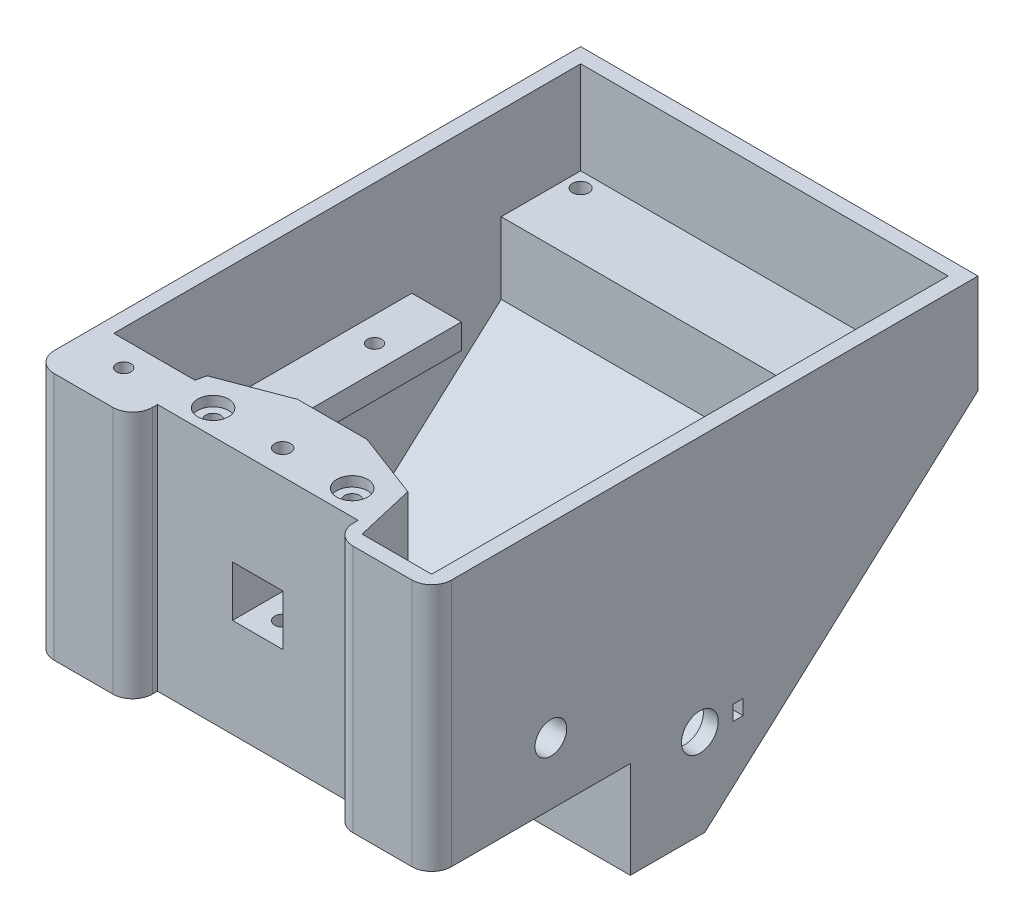
SolidWorks part; units mm, degrees
ref_plane "Спереди" through (0, 0, 0) normal (0, 0, 1) x (1, 0, 0)
ref_plane "Сверху" through (0, 0, 0) normal (0, 1, 0) x (1, 0, 0)
ref_plane "Справа" through (0, 0, 0) normal (1, 0, 0) x (0, 0, -1)
sketch "Sketch2" plane through (0, 0, 0) normal (1, 0, 0) x (0, 0, -1)
  line L0 (-27.3205, 20.9982) -> (-27.3205, -29.0018)
  line L1 (-27.3205, -29.0018) -> (12.6795, -29.0018)
  line L2 (12.6795, -29.0018) -> (12.6795, -48.5114)
  line L3 (12.6795, -48.5114) -> (27.6795, -48.5114)
  line L4 (82.6795, 20.9982) -> (82.6795, 0.9982)
  line L5 (82.6795, 20.9982) -> (-27.3205, 20.9982)
  line L6 (82.6795, 0.9982) -> (27.6795, -48.5114)
  dimension "D1" = 110
  dimension "D2" = 50
  dimension "D3" = 40
  dimension "D4" = 15
  dimension "D5" = 20
extrude "Boss-Extrude1" add sketch "Sketch2" along normal blind 80
shell "Shell1" thickness 3
sketch "Sketch3" plane through (0, 0, 24.3205) normal (0, 0, -1) x (-1, 0, 0)
  line L0 (-40, 20.9982) -> (-40, -26.0018) construction
  line L3 (-77, 20.9982) -> (-3, 20.9982) construction
  line L4 (-77, -26.0018) -> (-3, -26.0018) construction
  line L6 (-17, 20.9982) -> (-63, 20.9982)
  line L7 (-17, 20.9982) -> (-17, -26.0018)
  line L8 (-17, -26.0018) -> (-63, -26.0018)
  line L9 (-63, 20.9982) -> (-63, -26.0018)
  line L10 (-17, 20.9982) -> (-63, -26.0018) construction
  line L11 (-17, -26.0018) -> (-63, 20.9982) construction
  point P6 (-40, -2.5018)
  dimension "D1" = 46
extrude "Boss-Extrude2" add sketch "Sketch3" along normal blind 17
sketch "Sketch4" plane through (0, 0, 27.3205) normal (0, 0, 1) x (1, 0, 0)
  line L0 (0, 20.9982) -> (80, -29.0018) construction
  line L2 (45.1, -9.1018) -> (34.9, -9.1018)
  line L3 (45.1, -9.1018) -> (45.1, 1.0982)
  line L4 (45.1, 1.0982) -> (34.9, 1.0982)
  line L5 (34.9, -9.1018) -> (34.9, 1.0982)
  line L6 (45.1, -9.1018) -> (34.9, 1.0982) construction
  line L7 (45.1, 1.0982) -> (34.9, -9.1018) construction
  point P4 (40, -4.0018)
  dimension "D1" = 10.2
extrude "Cut-Extrude1" cut sketch "Sketch4" against normal up to surface (20 mm away) up to face at (40, -2.5018, 7.3205)
sketch "Sketch6" plane through (0, -29.0018, 0) normal (0, -1, 0) x (1, 0, 0)
  line L0 (40, 27.3205) -> (40, -12.6795) construction
  line L1 (47.5, -5.4795) -> (32.5, -5.4795)
  line L2 (47.5, -5.4795) -> (47.5, 7.3205)
  line L3 (47.5, 7.3205) -> (32.5, 7.3205)
  line L4 (32.5, -5.4795) -> (32.5, 7.3205)
  line L5 (47.5, -5.4795) -> (32.5, 7.3205) construction
  line L6 (47.5, 7.3205) -> (32.5, -5.4795) construction
  line L7 (80, -12.6795) -> (0, -12.6795) construction
  line L9 (80, 27.3205) -> (0, 27.3205) construction
  point P0 (40, 0.9205)
  dimension "D1" = 15
  dimension "D2" = 12.8
  dimension "D4" = 20
extrude "Cut-Extrude2" cut sketch "Sketch6" against normal up to surface (3 mm away) up to face at (40, -26.0018, 10.0705)
sketch "Sketch7" plane through (0, 0, 27.3205) normal (0, 0, 1) x (1, 0, 0)
  line L0 (40, 20.9982) -> (40, -29.0018) construction
  line L1 (80, 20.9982) -> (0, 20.9982) construction
  line L2 (80, -29.0018) -> (0, -29.0018) construction
  line L4 (60.2, -29.0018) -> (19.8, -29.0018)
  line L5 (60.2, -29.0018) -> (60.2, 20.9982)
  line L6 (60.2, 20.9982) -> (19.8, 20.9982)
  line L7 (19.8, -29.0018) -> (19.8, 20.9982)
  line L8 (60.2, -29.0018) -> (19.8, 20.9982) construction
  line L9 (60.2, 20.9982) -> (19.8, -29.0018) construction
  point P6 (40, -4.0018)
  dimension "D1" = 40.4
extrude "Cut-Extrude3" cut sketch "Sketch7" against normal blind 5
fillet "Fillet1" radius 4 4 edges at (19.8, -4.0018, 27.3205) (60.2, -4.0018, 27.3205) (80, -4.0018, 27.3205) (0, -4.0018, 27.3205)
sketch "Sketch12" plane through (0, 20.9982, 0) normal (0, 1, 0) x (1, 0, 0)
  line L0 (19.8, -22.3205) -> (19.8, -12.3205) construction
  line L1 (19.8, -12.3205) -> (60.2, -12.3205) construction
  line L2 (60.2, -12.3205) -> (60.2, -22.3205) construction
  line L3 (33, -7.3205) -> (19.8, -12.3205)
  line L4 (17, -7.3205) -> (63, -7.3205) construction
  line L5 (19.8, -12.3205) -> (17, -24.3205)
  line L6 (17, -24.3205) -> (17, -7.3205)
  line L7 (17, -7.3205) -> (33, -7.3205)
  line L8 (47, -7.3205) -> (63, -7.3205)
  line L9 (63, -7.3205) -> (63, -24.3205)
  line L10 (63, -24.3205) -> (60.2, -12.3205)
  line L11 (60.2, -12.3205) -> (47, -7.3205)
  dimension "D1" = 10
  dimension "D2" = 16
extrude "Cut-Extrude7" cut sketch "Sketch12" against normal up to surface (47 mm away) up to face at (40, -26.0018, 7.0205)
sketch "Sketch13" plane through (0, 20.9982, 0) normal (0, 1, 0) x (1, 0, 0)
  line L0 (19.8, -22.3205) -> (19.8, -12.3205) construction
  line L1 (19.8, -12.3205) -> (60.2, -12.3205) construction
  line L2 (60.2, -12.3205) -> (60.2, -22.3205) construction
  line L3 (60.2, -17.3205) -> (19.8, -17.3205) construction
  circle A0 centre (26, -17.3205) radius 1.5
  circle A1 centre (54, -17.3205) radius 1.5
  point P14 (40, -17.3205)
  dimension "D1" = 3
  dimension "D2" = 28
  dimension "D3" = 14
  dimension "D4" = 6.2
extrude "Cut-Extrude8" cut sketch "Sketch13" against normal blind 25
sketch "Sketch14" plane through (0, 20.9982, 0) normal (0, 1, 0) x (1, 0, 0)
  circle A0 centre (26, -17.3205) radius 3.1
  circle A1 centre (54, -17.3205) radius 3.1
  dimension "D1" = 6.2
extrude "Cut-Extrude9" cut sketch "Sketch14" against normal blind 2
sketch "Sketch17" plane through (77, 0, 0) normal (-1, 0, 0) x (0, 0, 1)
  line L0 (-45.6795, -2.0018) -> (-0.6795, -2.0018)
  line L1 (-0.6795, -2.0018) -> (-0.6795, -7.0018)
  line L2 (-0.6795, -7.0018) -> (-45.6795, -7.0018)
  line L3 (-45.6795, -7.0018) -> (-45.6795, -2.0018)
  line L4 (-79.6795, 20.9982) -> (24.3205, 20.9982) construction
  line L5 (-79.6795, 2.3342) -> (-79.6795, 20.9982) construction
  dimension "D1" = 45
  dimension "D2" = 5
  dimension "D3" = 23
  dimension "D4" = 34
extrude "Boss-Extrude5" add sketch "Sketch17" along normal up to surface (74 mm away) up to face at (3, -14.0994, -24.0865)
sketch "Sketch18" plane through (0, -2.0018, 0) normal (0, 1, 0) x (1, 0, 0)
  line L0 (40, 0.6795) -> (40, 45.6795) construction
  line L1 (3, 0.6795) -> (77, 0.6795) construction
  line L2 (3, 45.6795) -> (77, 45.6795) construction
  line L3 (77, 0.6795) -> (77, 45.6795) construction
  line L4 (13, 0.6795) -> (67, 0.6795)
  line L5 (13, 0.6795) -> (13, 45.6795)
  line L6 (13, 45.6795) -> (67, 45.6795)
  line L7 (67, 0.6795) -> (67, 45.6795)
  line L8 (13, 0.6795) -> (67, 45.6795) construction
  line L9 (13, 45.6795) -> (67, 0.6795) construction
  point P6 (40, 23.1795)
  dimension "D1" = 10
extrude "Cut-Extrude10" cut sketch "Sketch18" against normal up to next
sketch "Sketch19" plane through (0, -2.0018, 0) normal (0, 1, 0) x (1, 0, 0)
  line L0 (72, 45.6795) -> (72, 0.6795) construction
  line L1 (67, 45.6795) -> (77, 45.6795) construction
  line L2 (67, 0.6795) -> (77, 0.6795) construction
  line L3 (8, 45.6795) -> (8, 0.6795) construction
  line L4 (3, 45.6795) -> (13, 45.6795) construction
  line L5 (3, 0.6795) -> (13, 0.6795) construction
  circle A0 centre (72, 37.1795) radius 1.45
  circle A1 centre (72, 6.1795) radius 1.45
  circle A2 centre (8, 33.1795) radius 1.45
  circle A3 centre (8, 6.1795) radius 1.45
  point P20 (72, 23.1795)
  point P21 (8, 23.1795)
  dimension "D1" = 2.9
  dimension "D2" = 14
  dimension "D3" = 17
  dimension "D4" = 17
  dimension "D5" = 10
extrude "Cut-Extrude11" cut sketch "Sketch19" against normal up to next
sketch "Sketch21" plane through (0, -26.0018, 0) normal (0, 1, 0) x (1, 0, 0)
  line L0 (3, -24.3205) -> (3, -14.3205)
  line L1 (3, -24.3205) -> (3, 15.6795) construction
  line L2 (3, -14.3205) -> (19.3333, -14.3205)
  line L3 (19.8, -12.3205) -> (17, -24.3205) construction
  line L4 (19.3333, -14.3205) -> (17, -24.3205)
  line L6 (3, -24.3205) -> (17, -24.3205)
  dimension "D1" = 10
extrude "Boss-Extrude6" add sketch "Sketch21" along normal up to surface (47 mm away) up to face at (54, 20.9982, 20.4205)
sketch "Sketch22" plane through (0, 20.9982, 0) normal (0, 1, 0) x (1, 0, 0)
  line L0 (0, 82.6795) -> (0, -23.3205) construction
  line L1 (15.8, -27.3205) -> (4, -27.3205) construction
  circle A0 centre (10, -19.3205) radius 1.45
  dimension "D1" = 2.9
  dimension "D2" = 10
  dimension "D3" = 8
extrude "Cut-Extrude12" cut sketch "Sketch22" against normal through all
sketch "Sketch24" plane through (80, 0, 0) normal (1, 0, 0) x (0, 0, -1)
  line L0 (12.6795, -48.5114) -> (27.6795, -48.5114) construction
  line L1 (12.6795, -29.0018) -> (12.6795, -48.5114) construction
  line L2 (18.1795, -30.5114) -> (18.1795, -19.0114) construction
  line L3 (18.1795, -19.0114) -> (35.1795, -19.0114) construction
  line L4 (35.1795, -19.0114) -> (35.1795, -30.5114) construction
  line L5 (26.6795, -19.0114) -> (26.6795, -39.0114) construction
  line L6 (30.3795, -30.5114) -> (34.3795, -30.5114) construction
  line L8 (33.3795, -32.0114) -> (35.3795, -32.0114)
  line L9 (33.3795, -32.0114) -> (33.3795, -29.0114)
  line L10 (33.3795, -29.0114) -> (35.3795, -29.0114)
  line L11 (35.3795, -32.0114) -> (35.3795, -29.0114)
  line L12 (33.3795, -32.0114) -> (35.3795, -29.0114) construction
  line L13 (33.3795, -29.0114) -> (35.3795, -32.0114) construction
  circle A0 centre (26.6795, -30.5114) radius 3.7
  circle A1 centre (26.6795, -30.5114) radius 8.5 construction
  dimension "D1" = 7.4
  dimension "D2" = 17
  dimension "D3" = 18
  dimension "D4" = 14
  dimension "D5" = 20
  dimension "D6" = 4
  dimension "D7" = 2
  dimension "D8" = 3
extrude "Cut-Extrude13" cut sketch "Sketch24" against normal up to next
sketch "Sketch26" plane through (3, 0, 0) normal (1, 0, 0) x (0, 0, -1)
  line L0 (79.6795, 2.3342) -> (63.6795, 2.3342)
  line L1 (63.6795, 2.3342) -> (63.6795, -12.0686)
  line L2 (26.5281, -45.5114) -> (79.6795, 2.3342) construction
  line L3 (63.6795, -12.0686) -> (79.6795, 2.3342)
  dimension "D1" = 16
extrude "Boss-Extrude7" add sketch "Sketch26" along normal up to surface (74 mm away) up to face at (77, -30.5114, -34.3795)
sketch "Sketch27" plane through (0, 2.3342, 0) normal (0, 1, 0) x (1, 0, 0)
  line L0 (3, 76.6795) -> (77, 76.6795) construction
  line L1 (3, 79.6795) -> (3, 63.6795) construction
  line L2 (77, 79.6795) -> (77, 63.6795) construction
  line L3 (80, 82.6795) -> (0, 82.6795) construction
  circle A0 centre (6, 76.6795) radius 1.65
  circle A1 centre (74, 76.6795) radius 1.65
  point P10 (40, 76.6795)
  dimension "D1" = 3.3
  dimension "D2" = 68
  dimension "D3" = 34
  dimension "D4" = 6
extrude "Cut-Extrude14" cut sketch "Sketch27" against normal blind 10
sketch "Sketch28" plane through (0, 2.3342, 0) normal (0, 1, 0) x (1, 0, 0)
  line L1 (74, 79.9295) -> (71.1854, 78.3045)
  line L2 (71.1854, 78.3045) -> (71.1854, 75.0545)
  line L3 (71.1854, 75.0545) -> (74, 73.4295)
  line L4 (74, 73.4295) -> (76.8146, 75.0545)
  line L5 (76.8146, 75.0545) -> (76.8146, 78.3045)
  line L6 (76.8146, 78.3045) -> (74, 79.9295)
  line L7 (6, 73.4295) -> (8.8146, 75.0545)
  line L8 (8.8146, 75.0545) -> (8.8146, 78.3045)
  line L9 (8.8146, 78.3045) -> (6, 79.9295)
  line L10 (6, 79.9295) -> (3.1854, 78.3045)
  line L11 (3.1854, 78.3045) -> (3.1854, 75.0545)
  line L12 (3.1854, 75.0545) -> (6, 73.4295)
  circle A0 centre (74, 76.6795) radius 3.25 construction
  circle A1 centre (6, 76.6795) radius 3.25 construction
  dimension "D1" = 6.5
extrude "Cut-Extrude15" cut sketch "Sketch28" against normal blind 32 from offset 3 offset against normal yes
sketch "Sketch29" plane through (0, -29.0018, 0) normal (0, -1, 0) x (1, 0, 0)
  line L0 (0, 23.3205) -> (0, -12.6795) construction
  line L1 (7.1854, 17.6955) -> (10, 16.0705)
  line L2 (10, 16.0705) -> (12.8146, 17.6955)
  line L3 (12.8146, 17.6955) -> (12.8146, 20.9455)
  line L4 (12.8146, 20.9455) -> (10, 22.5705)
  line L5 (10, 22.5705) -> (7.1854, 20.9455)
  line L6 (7.1854, 20.9455) -> (7.1854, 17.6955)
  circle A0 centre (10, 19.3205) radius 3.25 construction
  dimension "D1" = 6.5
extrude "Cut-Extrude16" cut sketch "Sketch29" against normal blind 30
sketch "Sketch30" plane through (0, -26.0018, 0) normal (0, 1, 0) x (1, 0, 0)
  line L0 (77, -24.3205) -> (63, -24.3205)
  line L1 (63, -24.3205) -> (60.2, -12.3205)
  line L2 (63, -24.3205) -> (60.2, -12.3205) construction
  line L3 (60.2, -12.3205) -> (77, -12.3205)
  line L4 (77, -24.3205) -> (77, 15.6795) construction
  line L5 (77, -12.3205) -> (77, -24.3205)
  dimension "D1" = 12
extrude "Boss-Extrude8" add sketch "Sketch30" along normal blind 20
sketch "Sketch31" plane through (0, -6.0018, 0) normal (0, 1, 0) x (1, 0, 0)
  line L0 (76, -27.3205) -> (64.2, -27.3205) construction
  line L1 (80, -23.3205) -> (80, 12.6795) construction
  circle A0 centre (72, -21.3205) radius 1.5
  dimension "D3" = 3
  dimension "D1" = 6
  dimension "D2" = 8
extrude "Cut-Extrude17" cut sketch "Sketch31" against normal through all
sketch "Sketch32" plane through (0, -29.0018, 0) normal (0, -1, 0) x (1, 0, 0)
  line L1 (72, 24.5705) -> (69.1854, 22.9455)
  line L2 (69.1854, 22.9455) -> (69.1854, 19.6955)
  line L3 (69.1854, 19.6955) -> (72, 18.0705)
  line L4 (72, 18.0705) -> (74.8146, 19.6955)
  line L5 (74.8146, 19.6955) -> (74.8146, 22.9455)
  line L6 (74.8146, 22.9455) -> (72, 24.5705)
  circle A0 centre (72, 21.3205) radius 3.25 construction
  dimension "D1" = 6.5
extrude "Cut-Extrude18" cut sketch "Sketch32" against normal blind 15
sketch "Sketch33" plane through (0, -2.0018, 0) normal (0, 1, 0) x (1, 0, 0)
  line L0 (67, 40.6795) -> (77, 40.6795)
  line L1 (67, 0.6795) -> (67, 45.6795) construction
  line L2 (77, 0.6795) -> (77, 45.6795) construction
  line L3 (77, 40.6795) -> (77, 45.6795)
  line L4 (77, 45.6795) -> (67, 45.6795)
  line L5 (67, 45.6795) -> (67, 40.6795)
  dimension "D1" = 5
extrude "Cut-Extrude19" cut sketch "Sketch33" against normal up to next
sketch "Sketch34" plane through (0, 20.9982, 0) normal (0, 1, 0) x (1, 0, 0)
  line L0 (54, -17.3205) -> (26, -17.3205) construction
  circle A0 centre (40, -17.3205) radius 1.6
  dimension "D1" = 3.2
extrude "Cut-Extrude20" cut sketch "Sketch34" against normal through all
sketch "Sketch36" plane through (0, -29.0018, 0) normal (0, -1, 0) x (1, 0, 0)
  line L1 (38.375, 20.1351) -> (36.75, 17.3205)
  line L2 (36.75, 17.3205) -> (38.375, 14.5059)
  line L3 (38.375, 14.5059) -> (41.625, 14.5059)
  line L4 (41.625, 14.5059) -> (43.25, 17.3205)
  line L5 (43.25, 17.3205) -> (41.625, 20.1351)
  line L6 (41.625, 20.1351) -> (38.375, 20.1351)
  circle A0 centre (40, 17.3205) radius 3.25 construction
  dimension "D1" = 6.5
extrude "Cut-Extrude22" cut sketch "Sketch36" against normal blind 14
sketch "Sketch37" plane through (80, 0, 0) normal (1, 0, 0) x (0, 0, -1)
  line L0 (-23.3205, -16.5114) -> (63.2281, -16.5114) construction
  line L1 (-23.3205, 20.9982) -> (-23.3205, -29.0018) construction
  line L2 (27.6795, -48.5114) -> (82.6795, 0.9982) construction
  line L3 (30.3795, -30.5114) -> (22.9795, -30.5114) construction
  circle A0 centre (-3.3205, -16.5114) radius 3.2
  circle A1 centre (26.6795, -30.5114) radius 3.7 construction
  point P14 (26.6795, -30.5114)
  dimension "D1" = 6.4
  dimension "D2" = 14
  dimension "D3" = 20
extrude "Cut-Extrude23" cut sketch "Sketch37" against normal up to next
sketch "Sketch38" plane through (77, 0, 0) normal (-1, 0, 0) x (0, 0, 1)
  line L0 (12.3205, -26.0018) -> (-15.6795, -26.0018) construction
  line L1 (8.3205, -7.021) -> (-1.6795, -7.021)
  line L2 (8.3205, -7.021) -> (8.3205, -26.0018)
  line L3 (8.3205, -26.0018) -> (-1.6795, -26.0018)
  line L4 (-1.6795, -7.021) -> (-1.6795, -26.0018)
  line L5 (8.3205, -7.021) -> (-1.6795, -26.0018) construction
  line L6 (8.3205, -26.0018) -> (-1.6795, -7.021) construction
  circle A0 centre (3.3205, -16.5114) radius 3.2
  point P0 (3.3205, -16.5114)
  dimension "D1" = 10
extrude "Boss-Extrude9" add sketch "Sketch38" along normal blind 3
